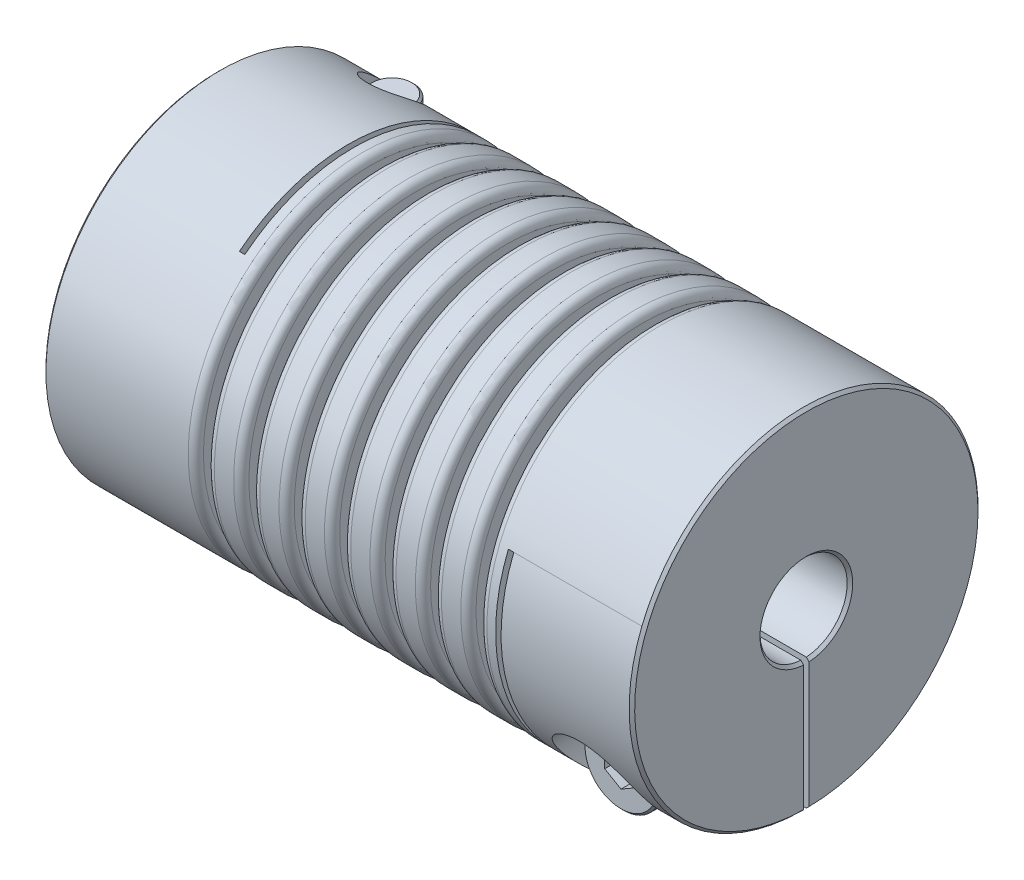
SolidWorks part; units mm, degrees
ref_plane "Front Plane" through (0, 0, 0) normal (0, 0, 1) x (1, 0, 0)
ref_plane "Top Plane" through (0, 0, 0) normal (0, 1, 0) x (1, 0, 0)
ref_plane "Right Plane" through (0, 0, 0) normal (1, 0, 0) x (0, 0, -1)
sketch "Sketch1" plane through (0, 0, 0) normal (1, 0, 0) x (0, 0, -1)
  circle A0 centre (0, 0) radius 16
  dimension "dim D" = 32
extrude "Boss-Extrude1" add sketch "Sketch1" along normal mid plane 54
sketch "Sketch2" plane through (27, 0, 0) normal (1, 0, 0) x (0, 0, -1)
  circle A0 centre (0, 0) radius 4
  dimension "dim D1" = 8
extrude "Cut-Extrude1" cut sketch "Sketch2" against normal through all
chamfer "Chamfer1" distance 0.254 angle 45 4 edges at (-27, 0, -4) (-27, 0, -16) (27, 0, -16) (27, 0, -4)
ref_plane "Plane2" through (0, -16, 0) normal (0, -1, 0) x (1, 0, 0)
ref_plane "F" through (-21, 0, 0) normal (-1, 0, 0) x (0, 0, 1)
sketch "Sketch4" plane through (0, -16, 0) normal (0, -1, 0) x (1, 0, 0)
  line L0 (-26.746, -16) -> (26.746, -16) construction
  line L1 (-15, -16) -> (-14.5, -16)
  line L2 (-15, -16) -> (-15, 10)
  line L3 (-15, 10) -> (-14.5, 10)
  line L4 (-14.5, -16) -> (-14.5, 10)
  line L5 (-15, 4) -> (-15, 16) construction
  line L6 (26.746, 4) -> (-26.746, 4) construction
  line L7 (26.746, 16) -> (-26.746, 16) construction
  line L10 (-15, 10) -> (-27, 10) construction
  line L11 (-27, 15.746) -> (-27, -15.746) construction
  line L12 (-21, 10.2256) -> (-21, -10.2256) construction
  point P16 (-21, 10)
  dimension "D1" = 0.5
extrude "Cut-Extrude2" cut sketch "Sketch4" against normal through all
ref_plane "Plane4" through (0, 0, -16) normal (0, 0, -1) x (-1, 0, 0)
sketch "Sketch7" plane through (0, 0, -16) normal (0, 0, -1) x (-1, 0, 0)
  line L1 (-14.5, -16) -> (-15, -16)
  line L2 (-15, -16) -> (-15, 6)
  line L3 (-15, 6) -> (-14.5, 6)
  line L4 (-14.5, -16) -> (-14.5, 6)
  line L5 (27, 8.6487) -> (21, 8.6487) construction
  line L7 (-10.505, -16) -> (10.505, -16) construction
  line L8 (-26.746, -4) -> (14.5, -4) construction
  line L9 (27, -15.746) -> (27, 15.746) construction
  line L10 (-26.746, -4) -> (14.5, -4) construction
  line L11 (14.5, 12.49) -> (15, 12.49) construction
  line L12 (-15, 6) -> (-15, -16) construction
  line L14 (-26.746, -4) -> (14.5, -4) construction
  line L16 (-26.746, -4) -> (14.5, -4) construction
  line L17 (15, -16) -> (26.746, -16) construction
  line L18 (21, -10.2256) -> (21, 10.2256) construction
  line L19 (-26.746, -16) -> (-26.746, 16) construction
  line L20 (-27, 6) -> (-21, 6) construction
  line L21 (-27, 15.746) -> (-27, -15.746) construction
  line L22 (-21, 6) -> (-15, 6) construction
  line L23 (-26.746, -16) -> (-26.746, 16) construction
  line L24 (-26.746, -4) -> (-26.746, 16) construction
  line L25 (-26.746, -4) -> (14.5, -4) construction
  point P23 (-15, 6)
  point P33 (-26.746, 6)
extrude "Cut-Extrude3" cut sketch "Sketch7" against normal through all
sketch "Sketch8" plane through (0, 0, 0) normal (0, 1, 0) x (1, 0, 0)
  line L0 (-15, -10) -> (-15, 16) construction
  line L1 (-27, 16) -> (-15, 16)
  line L2 (-27, 16) -> (-27, 0)
  line L3 (-27, 0) -> (-15, 0)
  line L4 (-15, 16) -> (-15, 0)
  line L5 (10.505, 16) -> (-10.505, 16) construction
  line L6 (-27, 15.746) -> (-27, -15.746) construction
extrude "Cut-Extrude5" cut sketch "Sketch8" against normal mid plane 0.5
sketch "Sketch13" plane through (0, 0, 0) normal (0, 0, 1) x (1, 0, 0)
  line L0 (27, -15.746) -> (27, 15.746) construction
  line L1 (15, -16) -> (27, -16)
  line L2 (15, -16) -> (15, 0)
  line L3 (15, 0) -> (27, 0)
  line L4 (27, -16) -> (27, 0)
extrude "Cut-Extrude6" cut sketch "Sketch13" against normal mid plane 0.5
hole_wizard "CBORE for M4 SHCS1" positions "Sketch12" profile "Sketch11" counterbore size "M4" standard "Ansi Metric" end condition through all
sketch "Sketch12" plane through (0, -16, 0) normal (0, -1, 0) x (1, 0, 0)
  line L0 (-21, 10.2256) -> (-21, -10.2256) construction
  line L1 (-15, -3.9922) -> (-15, -15.998) construction
  line L2 (-15, -3.9922) -> (-15, -15.998)
  line L3 (-15, -9.9951) -> (-21, -9.9951) construction
  point P0 (-21, -9.9951)
sketch "Sketch11" plane through (-21, -16, -9.9951) normal (1, 0, 0) x (0, 0, -1)
  line L0 (0, 0) -> (0, 32)
  line L1 (0, 32) -> (2.25, 32)
  line L3 (2.25, 32) -> (2.25, 9)
  line L4 (2.25, 9) -> (4, 9)
  line L5 (4, 9) -> (4, 0)
  line L7 (4, 0) -> (0, 0)
  line L11 (0, -6.35) -> (0, 107.95) construction
  dimension "Thru Hole Dia." = 4.5
  dimension "Thru Hole Depth" = 32
  dimension "C'Bore Dia." = 8
  dimension "C'Bore Depth" = 9
ref_plane "Plane5" through (0, 0, 16) normal (0, 0, 1) x (1, 0, 0)
hole_wizard "CBORE for M4 SHCS2" positions "Sketch15" profile "Sketch14" counterbore size "M4" standard "Ansi Metric" end condition through all
sketch "Sketch15" plane through (0, 0, 16) normal (0, 0, 1) x (1, 0, 0)
  line L0 (-25, -7) -> (-17, -7) construction
  line L1 (-25, -7) -> (-17, -7)
  line L5 (0, 0) -> (0, 16) construction
  line L6 (-15, 16) -> (-26.746, 16) construction
  line L8 (25, -7) -> (17, -7)
  line L9 (21, -7) -> (21, -9.9951) construction
  line L11 (21, -15.998) -> (21, -3.9922) construction
  line L12 (26.746, -15.998) -> (15, -15.998) construction
  line L13 (15, -3.9922) -> (26.746, -3.9922) construction
  point P0 (21, -9.9951)
sketch "Sketch14" plane through (21, -9.9951, 16) normal (1, 0, 0) x (0, -1, 0)
  line L0 (0, 0) -> (0, 32)
  line L1 (0, 32) -> (2.25, 32)
  line L3 (2.25, 32) -> (2.25, 9)
  line L4 (2.25, 9) -> (4, 9)
  line L5 (4, 9) -> (4, 0)
  line L7 (4, 0) -> (0, 0)
  line L11 (0, -6.35) -> (0, 107.95) construction
  dimension "Thru Hole Dia." = 4.5
  dimension "Thru Hole Depth" = 32
  dimension "C'Bore Dia." = 8
  dimension "C'Bore Depth" = 9
sketch "Sketch16" plane through (0, 0, 7) normal (0, 0, 1) x (1, 0, 0)
  circle A0 centre (21, -9.9951) radius 3.5
  dimension "screw dia" = 7
extrude "Boss-Extrude2" add sketch "Sketch16" along normal blind 4 separate body
sketch "Sketch17" plane through (0, 0, 7) normal (0, 0, -1) x (-1, 0, 0)
  circle A0 centre (-21, -9.9951) radius 2
  dimension "D1" = 4
extrude "Boss-Extrude3" add sketch "Sketch17" along normal blind 19
chamfer "Chamfer2" distance 0.2 angle 45 3 edges at (19, -9.9951, -12) (24.5, -9.9951, 7) (24.5, -9.9951, 11)
sketch "Sketch18" plane through (0, 0, 11) normal (0, 0, 1) x (1, 0, 0)
  line L1 (21, -11.7272) -> (22.5, -10.8611)
  line L2 (22.5, -10.8611) -> (22.5, -9.1291)
  line L3 (22.5, -9.1291) -> (21, -8.2631)
  line L4 (21, -8.2631) -> (19.5, -9.1291)
  line L5 (19.5, -9.1291) -> (19.5, -10.8611)
  line L6 (19.5, -10.8611) -> (21, -11.7272)
  circle A0 centre (21, -9.9951) radius 1.5 construction
  dimension "hex" = 3
extrude "Cut-Extrude7" cut sketch "Sketch18" against normal blind 1.5
mirror "Mirror1" about plane through (0, 0, 0) normal (1, 0, 0) of bodies 121
pattern_circular "CirPattern1" count 2 every 90 about axis through (0, 0, 0) along (1, 0, 0) of bodies 122 117
delete or keep bodies "Body-Delete1" type delete bodies bodies 122
sketch "Sketch19" plane through (0, 0, 0) normal (0, 0, 1) x (1, 0, 0)
  line L0 (-27, -10.5) -> (27, -10.5) construction
  line L1 (-27, 15.746) -> (-27, -15.746) construction
  line L2 (27, -15.744) -> (27, 15.746) construction
  line L3 (0, 0) -> (0, -10.5) construction
  line L4 (0, 0) -> (0, 10.5) construction
  line L5 (26.746, 16) -> (-14.5, 16) construction
  line L6 (-0.5, 16) -> (0.5, 16)
  line L7 (-0.5, 16) -> (-0.5, 10.5)
  line L8 (-0.5, 10.5) -> (0.5, 10.5)
  line L9 (0.5, 16) -> (0.5, 10.5)
  line L10 (3.6667, 16) -> (4.6667, 16)
  line L11 (3.6667, 16) -> (3.6667, 10.5)
  line L12 (3.6667, 10.5) -> (4.6667, 10.5)
  line L13 (4.6667, 16) -> (4.6667, 10.5)
  line L14 (7.8333, 16) -> (8.8333, 16)
  line L15 (7.8333, 16) -> (7.8333, 10.5)
  line L16 (7.8333, 10.5) -> (8.8333, 10.5)
  line L17 (8.8333, 16) -> (8.8333, 10.5)
  line L18 (12, 16) -> (13, 16)
  line L19 (12, 16) -> (12, 10.5)
  line L20 (12, 10.5) -> (13, 10.5)
  line L21 (13, 16) -> (13, 10.5)
  line L22 (-13, 16) -> (-13, 10.5)
  line L23 (-12, 10.5) -> (-13, 10.5)
  line L24 (-12, 16) -> (-12, 10.5)
  line L25 (-12, 16) -> (-13, 16)
  line L26 (-8.8333, 16) -> (-8.8333, 10.5)
  line L27 (-7.8333, 10.5) -> (-8.8333, 10.5)
  line L28 (-7.8333, 16) -> (-7.8333, 10.5)
  line L29 (-7.8333, 16) -> (-8.8333, 16)
  line L30 (-4.6667, 16) -> (-4.6667, 10.5)
  line L31 (-3.6667, 10.5) -> (-4.6667, 10.5)
  line L32 (-3.6667, 16) -> (-3.6667, 10.5)
  line L33 (-3.6667, 16) -> (-4.6667, 16)
  line L34 (0, 0) -> (-27, 0) construction
  dimension "D1" = 1
  dimension "Dim E" = 21
  dimension "Dim L1" = 14
  dimension "D2" = 4
revolve "Cut-Revolve1" cut sketch "Sketch19" angle 360 about L34
fillet "Fillet1" radius 0.7 14 edges at (-12, 16, 0) (-8.8333, 16, 0) (-7.8333, 16, 0) (-4.6667, 16, 0) (-0.5, 16, 0) (-3.6667, 16, 0) (0.5, 16, 0) (3.6667, 16, 0) (4.6667, 16, 0) (7.8333, 16, 0) (8.8333, 16, 0) (12, 16, 0) (13, 16, 0) (-13, 16, 0)
fillet "Fillet2" radius 0.1 14 edges at (12, 10.5, 0) (13, 10.5, 0) (7.8333, 10.5, 0) (8.8333, 10.5, 0) (3.6667, 10.5, 0) (4.6667, 10.5, 0) (-0.5, 10.5, 0) (0.5, 10.5, 0) (-4.6667, 10.5, 0) (-3.6667, 10.5, 0) (-8.8333, 10.5, 0) (-7.8333, 10.5, 0) (-13, 10.5, 0) (-12, 10.5, 0)
